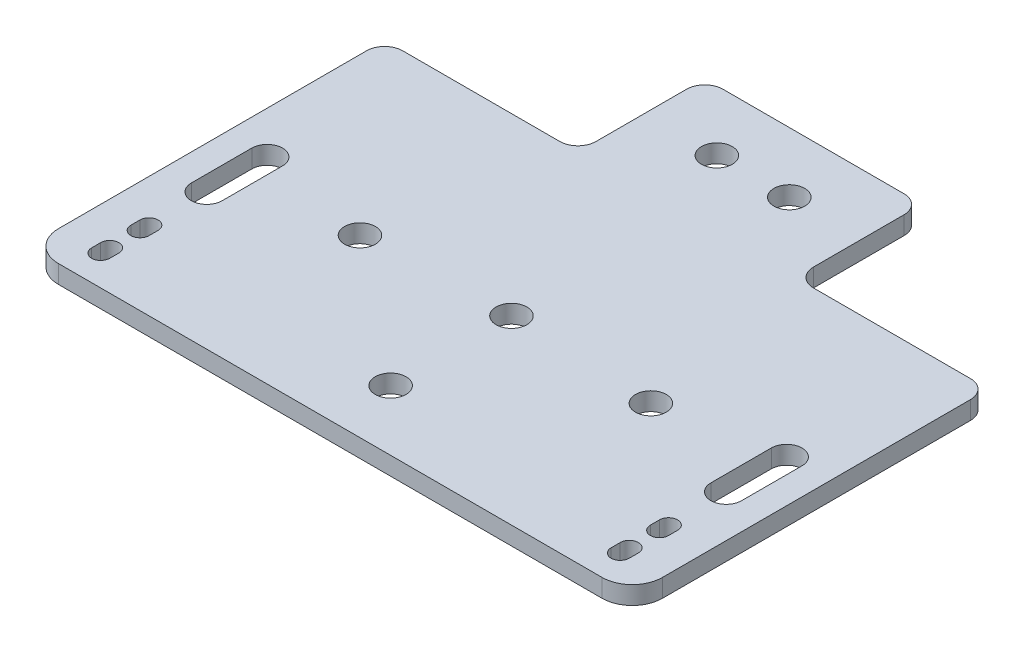
SolidWorks part; units mm, degrees
ref_plane "Front Plane" through (0, 0, 0) normal (0, 0, 1) x (1, 0, 0)
ref_plane "Top Plane" through (0, 0, 0) normal (0, 1, 0) x (1, 0, 0)
ref_plane "Right Plane" through (0, 0, 0) normal (1, 0, 0) x (0, 0, -1)
sketch "Sketch1" plane through (0, 0, 0) normal (0, 1, 0) x (1, 0, 0)
  line L0 (-19.3899, 28.2123) -> (10.6101, 28.2123)
  line L1 (13.6101, 25.2123) -> (13.6101, 10.2123)
  line L2 (16.6101, 7.2123) -> (32.6101, 7.2123)
  line L3 (-4.3899, 28.2123) -> (-4.3899, -51.7877) construction
  line L4 (38.6101, 7.2123) -> (38.6101, -51.7877) construction
  line L9 (-49.3899, -51.7877) -> (40.6101, -51.7877)
  line L10 (-41.3899, 7.2123) -> (-25.3899, 7.2123)
  line L11 (-22.3899, 10.2123) -> (-22.3899, 25.2123)
  line L14 (38.6101, -19.2293) -> (38.6101, -29.2293) construction
  line L16 (38.6101, -38.7877) -> (38.6101, -40.2877) construction
  line L17 (40.1101, -38.7877) -> (40.1101, -40.2877)
  line L18 (37.1101, -38.7877) -> (37.1101, -40.2877)
  line L19 (38.6101, -46.7877) -> (38.6101, -45.2877) construction
  line L20 (37.1101, -46.7877) -> (37.1101, -45.2877)
  line L21 (40.1101, -46.7877) -> (40.1101, -45.2877)
  line L24 (41.1601, -19.2293) -> (41.1601, -29.2293)
  line L27 (-47.3899, -38.7877) -> (-47.3899, -40.2877) construction
  line L28 (-45.8899, -38.7877) -> (-45.8899, -40.2877)
  line L29 (-48.8899, -38.7877) -> (-48.8899, -40.2877)
  line L30 (-47.3899, -46.7877) -> (-47.3899, -45.2877) construction
  line L31 (-48.8899, -46.7877) -> (-48.8899, -45.2877)
  line L32 (-45.8899, -46.7877) -> (-45.8899, -45.2877)
  line L34 (-41.3899, 7.2123) -> (-51.3899, 7.2123)
  line L35 (-54.3899, 4.2123) -> (-54.3899, -46.7877)
  line L37 (-47.3899, 7.2123) -> (-47.3899, -51.7877) construction
  line L38 (-47.3899, -19.2293) -> (-47.3899, -29.2293) construction
  line L39 (-44.8399, -19.2293) -> (-44.8399, -29.2293)
  line L40 (-49.9399, -19.2293) -> (-49.9399, -29.2293)
  line L41 (36.0601, -19.2293) -> (36.0601, -29.2293)
  line L42 (32.6101, 7.2123) -> (42.6101, 7.2123)
  line L43 (45.6101, 4.2123) -> (45.6101, -46.7877)
  arc A0 (-19.3899, 28.2123) -> (-22.3899, 25.2123) centre (-19.3899, 25.2123) ccw
  arc A1 (13.6101, 25.2123) -> (10.6101, 28.2123) centre (10.6101, 25.2123) ccw
  arc A2 (-54.3899, -46.7877) -> (-49.3899, -51.7877) centre (-49.3899, -46.7877) ccw
  arc A3 (-54.3899, 4.2123) -> (-51.3899, 7.2123) centre (-51.3899, 4.2123) cw
  arc A4 (42.6101, 7.2123) -> (45.6101, 4.2123) centre (42.6101, 4.2123) cw
  arc A5 (40.6101, -51.7877) -> (45.6101, -46.7877) centre (40.6101, -46.7877) ccw
  circle A6 centre (-10.3899, 18.2123) radius 2.55
  circle A7 centre (1.6101, 18.2123) radius 2.55
  circle A8 centre (-4.3899, -41.7877) radius 2.55
  circle A9 centre (-4.3899, -21.7877) radius 2.55
  arc A10 (16.6101, 7.2123) -> (13.6101, 10.2123) centre (16.6101, 10.2123) cw
  arc A11 (-25.3899, 7.2123) -> (-22.3899, 10.2123) centre (-25.3899, 10.2123) ccw
  circle A12 centre (-28.4699, -22.7877) radius 2.55
  circle A13 centre (19.6901, -22.7877) radius 2.55
  arc A14 (40.1101, -38.7877) -> (37.1101, -38.7877) centre (38.6101, -38.7877) ccw
  arc A15 (37.1101, -40.2877) -> (40.1101, -40.2877) centre (38.6101, -40.2877) ccw
  arc A16 (37.1101, -46.7877) -> (40.1101, -46.7877) centre (38.6101, -46.7877) ccw
  arc A17 (40.1101, -45.2877) -> (37.1101, -45.2877) centre (38.6101, -45.2877) ccw
  arc A18 (41.1601, -19.2293) -> (36.0601, -19.2293) centre (38.6101, -19.2293) ccw
  arc A19 (36.0601, -29.2293) -> (41.1601, -29.2293) centre (38.6101, -29.2293) ccw
  circle A20 centre (-28.4699, -22.7877) radius 10.5 construction
  circle A21 centre (19.6901, -22.7877) radius 10.5 construction
  arc A22 (-44.8399, -19.2293) -> (-49.9399, -19.2293) centre (-47.3899, -19.2293) ccw
  arc A23 (-49.9399, -29.2293) -> (-44.8399, -29.2293) centre (-47.3899, -29.2293) ccw
  arc A24 (-45.8899, -38.7877) -> (-48.8899, -38.7877) centre (-47.3899, -38.7877) ccw
  arc A25 (-48.8899, -40.2877) -> (-45.8899, -40.2877) centre (-47.3899, -40.2877) ccw
  arc A26 (-48.8899, -46.7877) -> (-45.8899, -46.7877) centre (-47.3899, -46.7877) ccw
  arc A27 (-45.8899, -45.2877) -> (-48.8899, -45.2877) centre (-47.3899, -45.2877) ccw
  point P14 (-22.3899, 28.2123)
  point P17 (13.6101, 28.2123)
  point P35 (13.6101, 7.2123)
  point P38 (-22.3899, 7.2123)
  point P57 (38.6101, -39.5377)
  point P62 (38.6101, -46.0377)
  point P70 (38.6101, -24.2293)
  point P88 (-47.3899, -39.5377)
  point P95 (-47.3899, -46.0377)
  point P103 (-47.3899, -24.2293)
  dimension "D4" = 3
  dimension "D5" = 3
  dimension "D7" = 7
  dimension "D8" = 5
  dimension "D9" = 7
  dimension "D10" = 12
  dimension "D11" = 59
  dimension "D14" = 3
  dimension "D15" = 10
  dimension "D12" = 20
  dimension "D16" = 1.5
  dimension "D17" = 5
  dimension "D23" = 25.92
  dimension "D24" = 5
  dimension "D20" = 80
  dimension "D25" = 2.55
  dimension "D26" = 5
  dimension "D21" = 5.1
  dimension "D22" = 3
  dimension "D18" = 5
  dimension "D19" = 10
  dimension "D1" = 36
  dimension "D3" = 21
  dimension "D6" = 100
  dimension "D13" = 10
other "AlignGroup1"
extrude "Boss-Extrude1" add sketch "Sketch1" along normal blind 3
